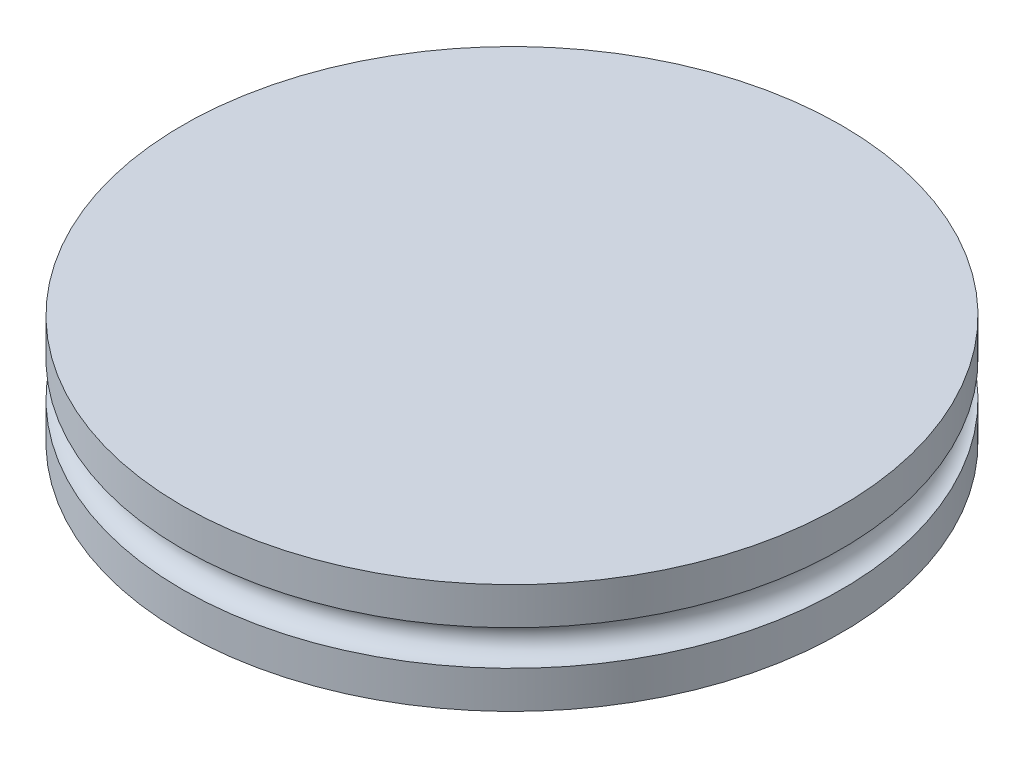
SolidWorks part; units mm, degrees
ref_plane "Front Plane" through (0, 0, 0) normal (0, 0, 1) x (1, 0, 0)
ref_plane "Top Plane" through (0, 0, 0) normal (0, 1, 0) x (1, 0, 0)
ref_plane "Right Plane" through (0, 0, 0) normal (1, 0, 0) x (0, 0, -1)
sketch "Sketch1" plane through (0, 0, 0) normal (0, 1, 0) x (1, 0, 0)
  circle A0 centre (0, 0) radius 9.525
extrude "Boss-Extrude1" add sketch "Sketch1" along normal blind 3.175
sketch "Sketch3" plane through (0, 0, 0) normal (0, 0, 1) x (1, 0, 0)
  line L0 (9.525, 3.175) -> (-9.525, 3.175) construction
  line L1 (-9.525, 3.175) -> (-9.525, 0) construction
  circle A0 centre (-8.509, 1.5875) radius 0.508
  dimension "D1" = 1.5875
  dimension "D2" = 1.016
extrude "Cut-Extrude1" cut sketch "Sketch3" against normal mid plane 50.8
sketch "Sketch4" plane through (0, 0, 0) normal (0, 0, 1) x (1, 0, 0)
  line L0 (9.525, 0) -> (9.525, 3.175) construction
  circle A0 centre (9.525, 1.5875) radius 0.508
sketch "Sketch5" plane through (0, 0, 0) normal (0, 1, 0) x (1, 0, 0)
  line L0 (0, 0) -> (-7.5548, -0.9946) construction
  line L1 (0, 0) -> (-7.5548, 0.9946) construction
  line L2 (0, 0) -> (-7.62, 0) construction
  arc A0 (-7.5548, -0.9946) -> (-7.5548, 0.9946) centre (0, 0) ccw
  dimension "D1" = 15
  dimension "D2" = 7.5
ref_plane "Plane1" through (0, 0, -7.62) normal (0, 0, 1) x (1, 0, 0)
ref_plane "Plane2" through (0, 0, 7.62) normal (0, 0, 1) x (1, 0, 0)
sketch "Sketch6" plane through (0, 0, -7.62) normal (0, 0, 1) x (1, 0, 0)
  line L1 (-8.509, 2.0955) -> (-9.525, 2.0955)
  line L2 (-8.509, 2.0955) -> (-8.509, 1.0795)
  line L3 (-8.509, 1.0795) -> (-9.525, 1.0795)
  line L4 (-9.525, 2.0955) -> (-9.525, 1.0795)
  line L5 (-9.525, 3.175) -> (-9.525, 0) construction
  circle A0 centre (-8.509, 1.5875) radius 0.508 construction
  point P6 (0, 0)
  point P7 (-9.525, 2.0955)
  dimension "D1" = 1.016
extrude "Cut-Extrude2" cut sketch "Sketch6" along normal blind 7.366
sketch "Sketch7" plane through (0, 0, 7.62) normal (0, 0, 1) x (1, 0, 0)
  line L0 (-9.5216, 1.0795) -> (-9.5216, 2.0955) construction
  line L1 (-8.509, 2.0955) -> (-9.5216, 2.0955)
  line L2 (-8.509, 2.0955) -> (-8.509, 1.0795)
  line L3 (-8.509, 1.0795) -> (-9.5216, 1.0795)
  line L4 (-9.5216, 2.0955) -> (-9.5216, 1.0795)
  circle A0 centre (-8.509, 1.5875) radius 0.508 construction
  arc A1 (-8.509, 2.0955) -> (-8.509, 1.0795) centre (-8.509, 1.5875) ccw construction
  point P6 (-9.5216, 2.0955)
  dimension "D1" = 1.016
extrude "Cut-Extrude3" cut sketch "Sketch7" against normal blind 7.366
sweep "Cut-Sweep1" cut profiles "Sketch4" path "Sketch5"
